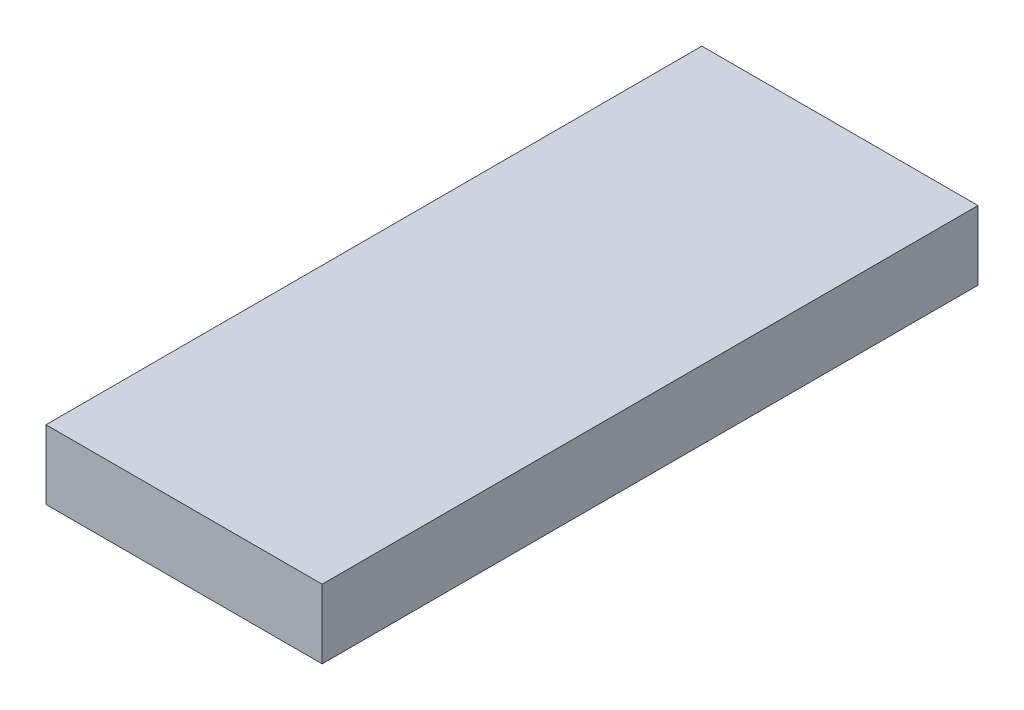
SolidWorks part; units mm, degrees
ref_plane "Plan de face" through (0, 0, 0) normal (0, 0, 1) x (1, 0, 0)
ref_plane "Plan de dessus" through (0, 0, 0) normal (0, 1, 0) x (1, 0, 0)
ref_plane "Plan de droite" through (0, 0, 0) normal (1, 0, 0) x (0, 0, -1)
sketch "Esquisse1" plane through (0, 0, 0) normal (0, 0, 1) x (1, 0, 0)
  line L0 (-4, 0) -> (4, 0)
  line L1 (4, 0) -> (4, -2)
  line L2 (4, -2) -> (2.5, -3.5)
  line L3 (2.5, -3.5) -> (-2.5, -3.5)
  line L4 (-2.5, -3.5) -> (-4, -2)
  line L5 (-4, -2) -> (-4, 0)
  line L6 (-4, -2) -> (4, -2) construction
  line L7 (0, 0) -> (0, -3.5) construction
  point P8 (0, 0)
  dimension "D1" = 2
  dimension "D2" = 8
  dimension "D3" = 1.5
extrude "Boss.-Extru.1" add sketch "Esquisse1" along normal blind 19
chamfer "Chanfrein1" distance 1.5 angle 45 2 edges at (0, -3.5, 0) (0, -3.5, 19)
